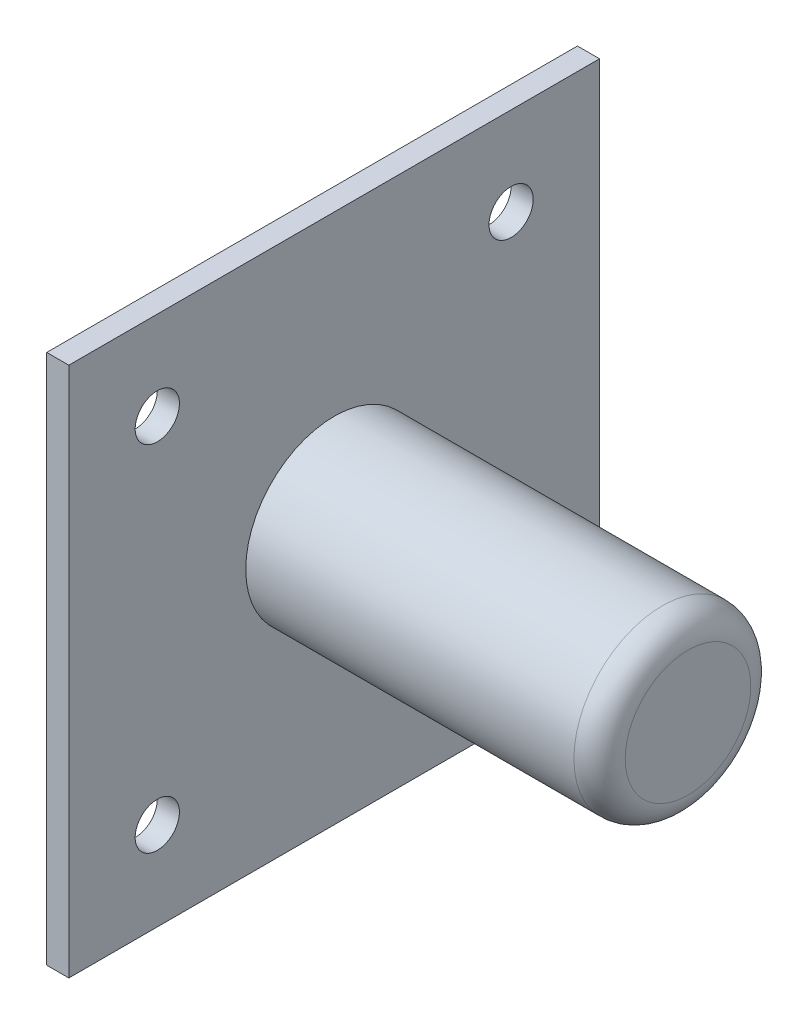
SolidWorks part; units mm, degrees
ref_plane "Front Plane" through (0, 0, 0) normal (0, 0, 1) x (1, 0, 0)
ref_plane "Top Plane" through (0, 0, 0) normal (0, 1, 0) x (1, 0, 0)
ref_plane "Right Plane" through (0, 0, 0) normal (1, 0, 0) x (0, 0, -1)
sketch "Sketch1" plane through (0, 0, 0) normal (1, 0, 0) x (0, 0, -1)
  line L1 (-38.1, -38.1) -> (38.1, -38.1)
  line L2 (-38.1, -38.1) -> (-38.1, 38.1)
  line L3 (-38.1, 38.1) -> (38.1, 38.1)
  line L4 (38.1, -38.1) -> (38.1, 38.1)
  line L5 (-38.1, -38.1) -> (38.1, 38.1) construction
  line L6 (-38.1, 38.1) -> (38.1, -38.1) construction
  line L7 (25.4, -25.4) -> (-25.4, -25.4) construction
  line L8 (25.4, -25.4) -> (25.4, 25.4) construction
  line L9 (25.4, 25.4) -> (-25.4, 25.4) construction
  line L10 (-25.4, -25.4) -> (-25.4, 25.4) construction
  line L11 (25.4, -25.4) -> (-25.4, 25.4) construction
  line L12 (25.4, 25.4) -> (-25.4, -25.4) construction
  circle A0 centre (-25.4, 25.4) radius 3.175
  circle A1 centre (25.4, 25.4) radius 3.175
  circle A2 centre (25.4, -25.4) radius 3.175
  circle A3 centre (-25.4, -25.4) radius 3.175
  point P0 (0, 0)
  point P14 (0, 0)
  dimension "D3" = 6.35
  dimension "D1" = 76.2
  dimension "D2" = 12.7
extrude "Boss-Extrude1" add sketch "Sketch1" along normal mid plane 3.175
sketch "Sketch2" plane through (0, 0, 0) normal (0, 0, 1) x (1, 0, 0)
  line L0 (1.5875, 38.1) -> (1.5875, -38.1) construction
  line L1 (1.5875, 38.1) -> (1.5875, -38.1)
  line L2 (1.5875, 12.7) -> (48.7042, 12.7)
  line L3 (1.5875, 0) -> (114.692, 0) construction
  line L5 (52.3875, 9.0167) -> (52.3875, 0)
  arc A0 (48.7042, 12.7) -> (52.3875, 9.0167) centre (48.7042, 9.0167) cw
  dimension "D1" = 50.8
  dimension "D2" = 12.7
revolve "Revolve1" add sketch "Sketch2" angle 360 about L3
